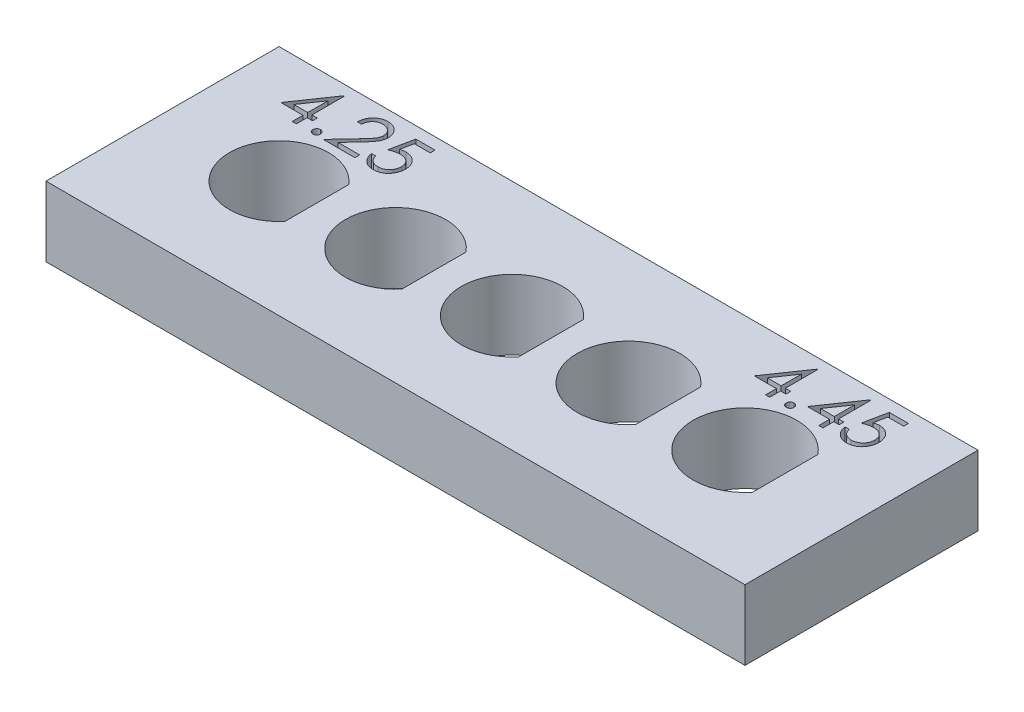
SolidWorks part; units mm, degrees
material "ABS"
ref_plane "Front Plane" through (0, 0, 0) normal (0, 0, 1) x (1, 0, 0)
ref_plane "Top Plane" through (0, 0, 0) normal (0, 1, 0) x (1, 0, 0)
ref_plane "Right Plane" through (0, 0, 0) normal (1, 0, 0) x (0, 0, -1)
sketch "Sketch1" plane through (0, 0, 0) normal (0, 1, 0) x (1, 0, 0)
  line L0 (-10, 0) -> (-15, 0) construction
  line L1 (0, -5) -> (0, 5) construction
  line L2 (-15, 5) -> (15, 5)
  line L3 (-15, 5) -> (-15, -5)
  line L4 (-15, -5) -> (15, -5)
  line L5 (15, 5) -> (15, -5)
  line L6 (-10, 0) -> (-5, 0) construction
  line L7 (-10, -2.125) -> (-10, 2.125) construction
  line L8 (-10, 0) -> (-12.125, 0)
  line L9 (-8.375, 1.3693) -> (-8.375, -1.3693)
  line L10 (-5, 0) -> (0, 0) construction
  line L11 (-5, -2.15) -> (-5, 2.15) construction
  line L12 (-5, 0) -> (-7.15, 0)
  line L13 (-3.35, 1.3784) -> (-3.35, -1.3784)
  line L14 (0, 0) -> (5, 0) construction
  line L15 (0, -2.175) -> (0, 2.175) construction
  line L16 (0, 0) -> (-2.175, 0)
  line L17 (1.675, 1.3874) -> (1.675, -1.3874)
  line L18 (5, 0) -> (10, 0) construction
  line L19 (5, -2.2) -> (5, 2.2) construction
  line L20 (5, 0) -> (2.8, 0)
  line L21 (6.7, 1.3964) -> (6.7, -1.3964)
  line L22 (10, 0) -> (21.9024, 0) construction
  line L23 (10, -2.225) -> (10, 2.225) construction
  line L24 (10, 0) -> (7.775, 0)
  line L25 (11.725, 1.4053) -> (11.725, -1.4053)
  arc A0 (-8.375, 1.3693) -> (-8.375, -1.3693) centre (-10, 0) ccw
  arc A1 (-3.35, 1.3784) -> (-3.35, -1.3784) centre (-5, 0) ccw
  arc A2 (1.675, 1.3874) -> (1.675, -1.3874) centre (0, 0) ccw
  arc A3 (6.7, 1.3964) -> (6.7, -1.3964) centre (5, 0) ccw
  arc A4 (11.725, 1.4053) -> (11.725, -1.4053) centre (10, 0) ccw
extrude "Boss-Extrude1" add sketch "Sketch1" against normal blind 3 contours L5 L2 L3 L4 A4 L25 A3 L21 A2 L17 A1 L13 A0 L9
sketch "Sketch2" plane through (0, 0, 0) normal (0, 1, 0) x (1, 0, 0)
  line L0 (-12.959, 2.5) -> (-6.9842, 2.5) construction
  line L5 (-15, 5) -> (-15, -5) construction
  line L8 (-12.959, 2.5) -> (-15, 2.5) construction
  line L11 (7.3596, 2.5) -> (13.4544, 2.5) construction
  text T0 "4.25\r\n\r\n" font "Century Gothic" height 2
  text T1 "4.45" font "Century Gothic" height 2
  dimension "D1" = 2.5
extrude "Cut-Extrude1" cut sketch "Sketch2" against normal blind 1
equation "\"D5@Sketch1\"=\"D1@Sketch1\"/6"
